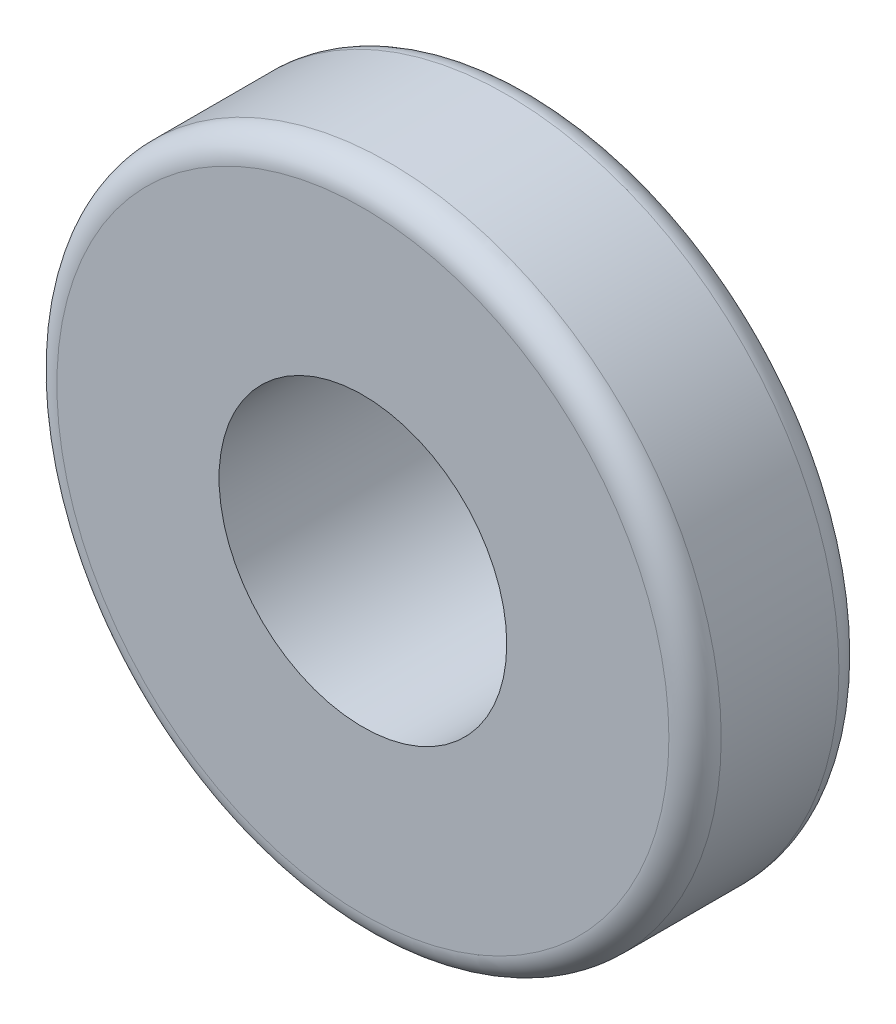
SolidWorks part; units mm, degrees
ref_plane "Front Plane" through (0, 0, 0) normal (0, 0, 1) x (1, 0, 0)
ref_plane "Top Plane" through (0, 0, 0) normal (0, 1, 0) x (1, 0, 0)
ref_plane "Right Plane" through (0, 0, 0) normal (1, 0, 0) x (0, 0, -1)
sketch "Sketch1" plane through (0, 0, 0) normal (0, 0, 1) x (1, 0, 0)
  circle A0 centre (0, 0) radius 127
  dimension "D1" = 254
extrude "Tire" add sketch "Sketch1" along normal blind 65
fillet "Fillet1" radius 10 2 edges at (127, 0, 0) (127, 0, 65)
sketch "Sketch5" plane through (0, 0, 0) normal (0, 0, -1) x (-1, 0, 0)
  circle A0 centre (0, 0) radius 67.5
  dimension "D1" = 135
extrude "Tire_Rim_Extrusion" add sketch "Sketch5" along normal blind 35
fillet "Fillet4" radius 10 1 edges at (-67.5, 0, -35)
sketch "Sketch6" plane through (0, 0, 65) normal (0, 0, 1) x (1, 0, 0)
  circle A0 centre (0, 0) radius 55
  dimension "D1" = 110
extrude "Tire_Hollow_Cut" cut sketch "Sketch6" against normal blind 85
sketch "Sketch7" plane through (0, 0, -20) normal (0, 0, 1) x (1, 0, 0)
  circle A0 centre (0, 0) radius 22.5
  circle A1 centre (0, 0) radius 17.5
  dimension "D1" = 45
  dimension "D2" = 35
extrude "Tire_Spline_Housing" add sketch "Sketch7" along normal blind 14.5 separate body
